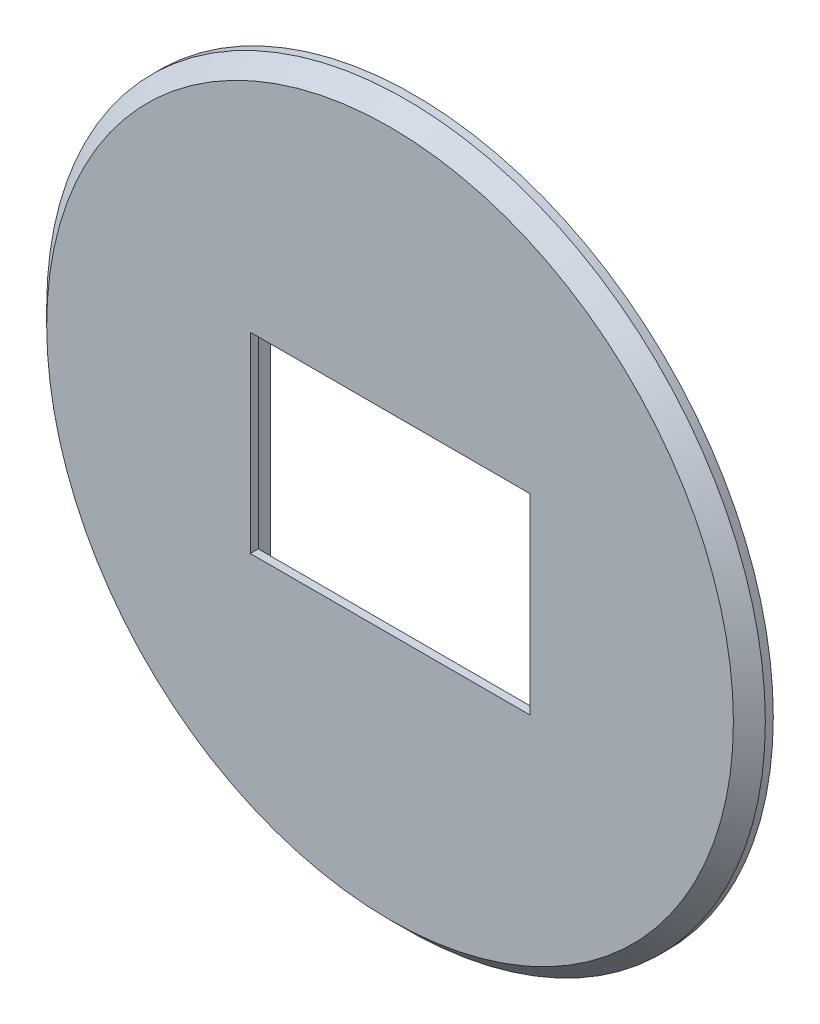
SolidWorks part; units mm, degrees
ref_plane "Front Plane" through (0, 0, 0) normal (0, 0, 1) x (1, 0, 0)
ref_plane "Top Plane" through (0, 0, 0) normal (0, 1, 0) x (1, 0, 0)
ref_plane "Right Plane" through (0, 0, 0) normal (1, 0, 0) x (0, 0, -1)
sketch "Sketch1" plane through (0, 0, 0) normal (0, 0, 1) x (1, 0, 0)
  circle A0 centre (0, 0) radius 45
  dimension "D1" = 90
extrude "Boss-Extrude1" add sketch "Sketch1" along normal blind 3
sketch "Sketch2" plane through (0, 0, 3) normal (0, 0, 1) x (1, 0, 0)
  line L1 (-17.5, 12) -> (17.5, 12)
  line L2 (-17.5, 12) -> (-17.5, -12)
  line L3 (-17.5, -12) -> (17.5, -12)
  line L4 (17.5, 12) -> (17.5, -12)
  line L5 (-17.5, 12) -> (17.5, -12) construction
  line L6 (-17.5, -12) -> (17.5, 12) construction
  point P0 (0, 0)
  dimension "D1" = 24
  dimension "D2" = 35
extrude "Cut-Extrude1" cut sketch "Sketch2" against normal blind 3
chamfer "Chamfer1" distance 2 angle 45 1 edges at (45, 0, 3)
sketch "Sketch3" plane through (0, 0, 0) normal (0, 0, -1) x (-1, 0, 0)
  line L1 (-18, 17) -> (18, 17)
  line L2 (-18, 17) -> (-18, -17)
  line L3 (-18, -17) -> (18, -17)
  line L4 (18, 17) -> (18, -17)
  line L5 (-18, 17) -> (18, -17) construction
  line L6 (-18, -17) -> (18, 17) construction
  point P0 (0, 0)
  dimension "D1" = 34
  dimension "D2" = 36
extrude "Cut-Extrude2" cut sketch "Sketch3" against normal blind 2
